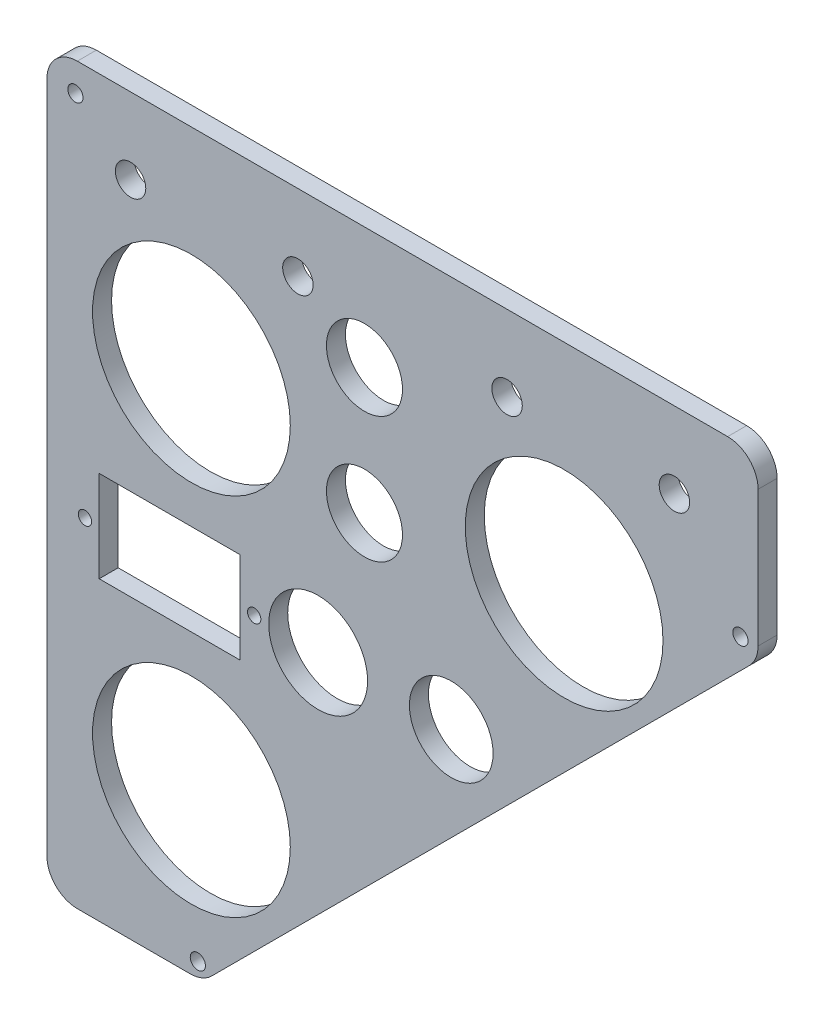
SolidWorks part; units mm, degrees
ref_plane "Piano frontale" through (0, 0, 0) normal (0, 0, 1) x (1, 0, 0)
ref_plane "Piano superiore" through (0, 0, 0) normal (0, 1, 0) x (1, 0, 0)
ref_plane "Piano destro" through (0, 0, 0) normal (1, 0, 0) x (0, 0, -1)
sketch "Schizzo1" plane through (0, 0, 0) normal (0, 0, 1) x (1, 0, 0)
  line L0 (0, 8) -> (0, 185)
  line L1 (8, 193) -> (179, 193)
  line L2 (187, 185) -> (187, 149.3137)
  line L3 (184.6569, 143.6569) -> (43.3431, 2.3431)
  line L4 (37.6863, 0) -> (8, 0)
  arc A0 (0, 185) -> (8, 193) centre (8, 185) cw
  arc A1 (0, 8) -> (8, 0) centre (8, 8) ccw
  arc A2 (43.3431, 2.3431) -> (37.6863, 0) centre (37.6863, 8) cw
  arc A3 (187, 149.3137) -> (184.6569, 143.6569) centre (179, 149.3137) cw
  arc A4 (179, 193) -> (187, 185) centre (179, 185) cw
  point P8 (0, 193)
  point P11 (0, 0)
  point P14 (41, 0)
  point P17 (187, 146)
  point P20 (187, 193)
  dimension "D5" = 8
  dimension "D1" = 187
  dimension "D2" = 47
  dimension "D3" = 45
  dimension "D4" = 193
extrude "Estrusione-Estrusione1" add sketch "Schizzo1" along normal blind 5
sketch "Schizzo5" plane through (0, 0, 5) normal (0, 0, 1) x (1, 0, 0)
  line L0 (13.75, 78) -> (13.75, 102)
  line L1 (50.75, 78) -> (13.75, 78)
  line L2 (50.75, 102) -> (50.75, 78)
  line L3 (13.75, 102) -> (50.75, 102)
  line L4 (179, 193) -> (8, 193) construction
  line L5 (187, 149.3137) -> (187, 185) construction
  line L6 (0, 185) -> (0, 8) construction
  line L7 (83.5, 161) -> (83.5, 127.8501) construction
  circle A1 centre (10, 90) radius 1.75
  circle A2 centre (54.5, 90) radius 1.75
  circle A3 centre (83.5, 161) radius 10
  circle A4 centre (106.3195, 90) radius 11
  circle A5 centre (71.3195, 90) radius 13
  circle A16 centre (10.4, 9.89) radius 2.25 construction
  circle A17 centre (38, 138) radius 26
  circle A18 centre (136, 138) radius 26
  circle A19 centre (38, 42) radius 26
  circle A20 centre (83.5, 127.8501) radius 10
  point P17 (13.75, 90)
  dimension "D4" = 32
  dimension "D7" = 80.6805
  dimension "interruttore" = 20
  dimension "D16" = 24
  dimension "D17" = 38
  dimension "D6" = 26
  dimension "D10" = 52
  dimension "D20" = 3.5
  dimension "D27" = 20
  dimension "D3" = 22
  dimension "D5" = 35
  dimension "D8" = 55
  dimension "D9" = 98
  dimension "D11" = 96
  dimension "D12" = 52.5
  dimension "D13" = 37
  dimension "D14" = 3.75
  dimension "D15" = 3.75
  dimension "D18" = 48
  dimension "D19" = 10
  dimension "D25" = 33.1499
extrude "Taglio-Estrusione2" cut sketch "Schizzo5" against normal blind 7
sketch "Schizzo6" plane through (0, 0, 5) normal (0, 0, 1) x (1, 0, 0)
  line L0 (165, 173) -> (22, 173) construction
  line L1 (179, 193) -> (8, 193) construction
  circle A0 centre (22, 173) radius 4
  circle A1 centre (66, 173) radius 4
  circle A2 centre (121, 173) radius 4
  circle A3 centre (165, 173) radius 4
  circle A4 centre (38, 138) radius 26 construction
  point P8 (93.5, 173)
  point P11 (93.5, 193)
  dimension "D1" = 8
  dimension "D2" = 55
  dimension "D3" = 44
  dimension "D4" = 35
  dimension "D6" = 44
extrude "Taglio-Estrusione3" cut sketch "Schizzo6" against normal blind 10
hole_wizard "Fori Alesato Ø4.0mm1" positions "Schizzo9" profile "Schizzo10" hole size "Ø4.0" standard "ISO"
sketch "Schizzo9" plane through (0, 0, 0) normal (0, 0, -1) x (-1, 0, 0)
  line L2 (-187, 149.3137) -> (-187, 185) construction
  line L3 (-179, 193) -> (-8, 193) construction
  point P0 (-182.36, 149.12)
  point P26 (-7.5, 185.4)
  point P28 (-39.69, 3.83)
  dimension "D1" = 174.86
  dimension "D2" = 36.28
  dimension "D3" = 181.57
  dimension "D4" = 32.19
  dimension "D5" = 4.64
  dimension "D6" = 43.88
sketch "Schizzo10" plane through (182.36, 149.12, 0) normal (1, 0, 0) x (0, 1, 0)
  line L0 (0, 0) -> (0, 41.8017)
  line L1 (0, 41.8017) -> (2, 40.6)
  line L2 (2, 40.6) -> (2, 0.025)
  line L3 (2, 0.025) -> (2.025, 0)
  line L5 (2.025, 0) -> (0, 0)
  line L6 (-2, 0.025) -> (-2.025, 0) construction
  line L10 (0, 41.8017) -> (-2, 40.6) construction
  line L11 (0, -6.35) -> (0, 107.95) construction
  dimension "Hole Dia." = 4
  dimension "Hole Depth" = 40.6
  dimension "Near C'Sink Dia." = 4.05
  dimension "Near C'Sink Angle" = 90
  dimension "Drill Angle" = 118
